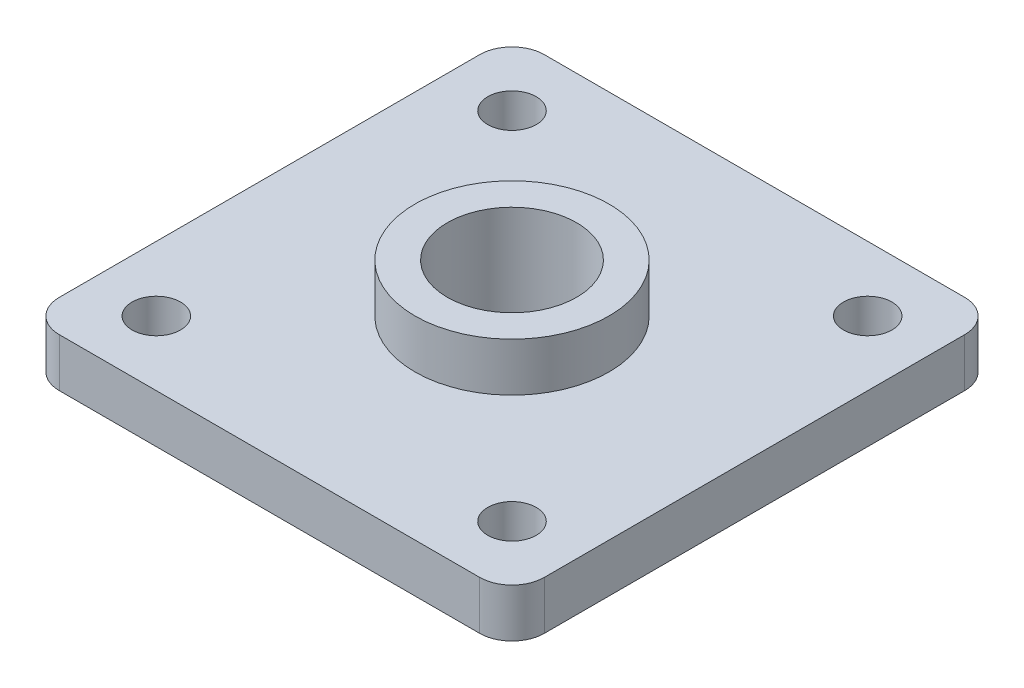
SolidWorks part; units mm, degrees
ref_plane "Front" through (0, 0, 0) normal (0, 0, 1) x (1, 0, 0)
ref_plane "Top" through (0, 0, 0) normal (0, 1, 0) x (1, 0, 0)
ref_plane "Right" through (0, 0, 0) normal (1, 0, 0) x (0, 0, -1)
sketch "Sketch1" plane through (0, 0, 0) normal (0, 1, 0) x (1, 0, 0)
  line L0 (-47.625, 0) -> (47.625, 0) construction
  line L1 (-47.625, 47.625) -> (47.625, 47.625)
  line L2 (-47.625, 47.625) -> (-47.625, -47.625)
  line L3 (-47.625, -47.625) -> (47.625, -47.625)
  line L4 (47.625, 47.625) -> (47.625, -47.625)
  dimension "D1" = 95.25
extrude "Extrude1" add sketch "Sketch1" along normal blind 9.525
sketch "Sketch2" plane through (0, 9.525, 0) normal (0, 1, 0) x (-1, 0, 0)
  circle A0 centre (0, 0) radius 19.05
  dimension "D1" = 38.1
extrude "Extrude2" add sketch "Sketch2" along normal blind 9.525
sketch "Sketch3" plane through (0, 19.05, 0) normal (0, 1, 0) x (-1, 0, 0)
  circle A0 centre (0, 0) radius 12.7
  circle A1 centre (0, 0) radius 19.05 construction
  dimension "D1" = 25.4
extrude "Cut-Extrude1" cut sketch "Sketch3" against normal through all
fillet "Fillet1" radius 6.35 4 edges at (-47.625, 4.7625, -47.625) (47.625, 4.7625, -47.625) (-47.625, 4.7625, 47.625) (47.625, 4.7625, 47.625)
sketch "Sketch4" plane through (0, 9.525, 0) normal (0, 1, 0) x (-1, 0, 0)
  line L0 (-34.925, -34.925) -> (-34.925, 34.925) construction
  line L1 (-34.925, 34.925) -> (34.925, 34.925) construction
  line L2 (34.925, 34.925) -> (34.925, -34.925) construction
  line L3 (34.925, -34.925) -> (-34.925, -34.925) construction
  line L4 (34.925, 0) -> (-34.925, 0) construction
  circle A0 centre (-34.925, -34.925) radius 4.7625
  circle A1 centre (34.925, -34.925) radius 4.7625
  circle A2 centre (34.925, 34.925) radius 4.7625
  circle A3 centre (-34.925, 34.925) radius 4.7625
  dimension "D2" = 9.525
  dimension "D1" = 69.85
extrude "Cut-Extrude2" cut sketch "Sketch4" against normal up to next
